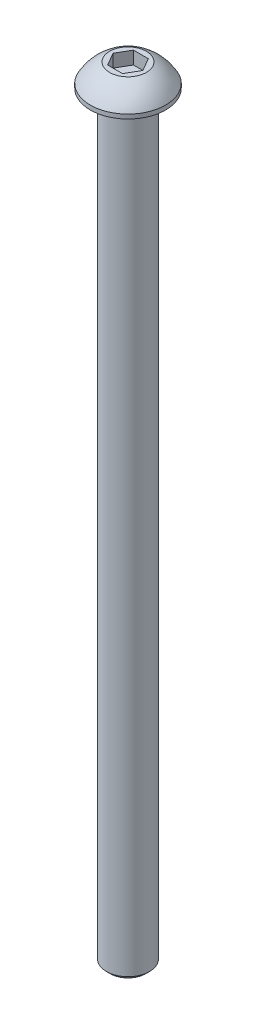
SolidWorks part; units mm, degrees
ref_plane "Front" through (0, 0, 0) normal (0, 0, 1) x (1, 0, 0)
ref_plane "Top" through (0, 0, 0) normal (0, 1, 0) x (1, 0, 0)
ref_plane "Right" through (0, 0, 0) normal (1, 0, 0) x (0, 0, -1)
sketch "Sketch1" plane through (0, 0, 0) normal (0, 0, 1) x (1, 0, 0)
  line L0 (0, 69.088) -> (0, -143.256) construction
  line L1 (0, -139.7) -> (3.2632, -139.7)
  line L2 (3.2632, -139.7) -> (3.9688, -138.9944)
  line L3 (3.9688, -138.9944) -> (3.9688, 0)
  line L4 (3.9688, 0) -> (6.9469, 0)
  line L5 (6.9469, 0) -> (6.9469, 0.7874)
  line L6 (3.3846, 4.2164) -> (0, 4.2164)
  line L7 (0, 4.2164) -> (0, -139.7)
  line L9 (2.7496, 4.2164) -> (1.3748, 6.5976) construction
  line L10 (1.3748, 6.5976) -> (-1.3748, 6.5976) construction
  line L11 (-1.3748, 6.5976) -> (-2.7496, 4.2164) construction
  line L12 (-2.7496, 4.2164) -> (-1.3748, 1.8351) construction
  line L13 (-1.3748, 1.8351) -> (1.3748, 1.8352) construction
  line L14 (1.3748, 1.8352) -> (2.7496, 4.2164) construction
  arc A0 (6.9469, 0.7874) -> (3.3846, 4.2164) centre (0, -2.8646) ccw
  circle A1 centre (0, 4.2164) radius 2.3813 construction
  dimension "D1" = 45
  dimension "Pitch" = 0.7056
  dimension "Dia" = 7.9375
  dimension "Length" = 139.7
  dimension "Rib" = 0.7874
  dimension "Height" = 4.2164
  dimension "HeadDia" = 13.8938
  dimension "HexW" = 4.7625
  dimension "D9" = 0.635
revolve "Base-Revolve" add sketch "Sketch1" angle 360 about L0
sketch "Sketch2" plane through (0, 4.2164, 0) normal (0, 1, 0) x (-1, 0, 0)
  line L1 (-2.7496, 0) -> (-1.3748, -2.3812)
  line L2 (-1.3748, -2.3812) -> (1.3748, -2.3812)
  line L3 (1.3748, -2.3812) -> (2.7496, 0)
  line L4 (2.7496, 0) -> (1.3748, 2.3812)
  line L5 (1.3748, 2.3812) -> (-1.3748, 2.3812)
  line L6 (-1.3748, 2.3812) -> (-2.7496, 0)
  circle A0 centre (0, 0) radius 2.3812 construction
extrude "Cut-Extrude1" cut sketch "Sketch2" against normal blind 2.3813
